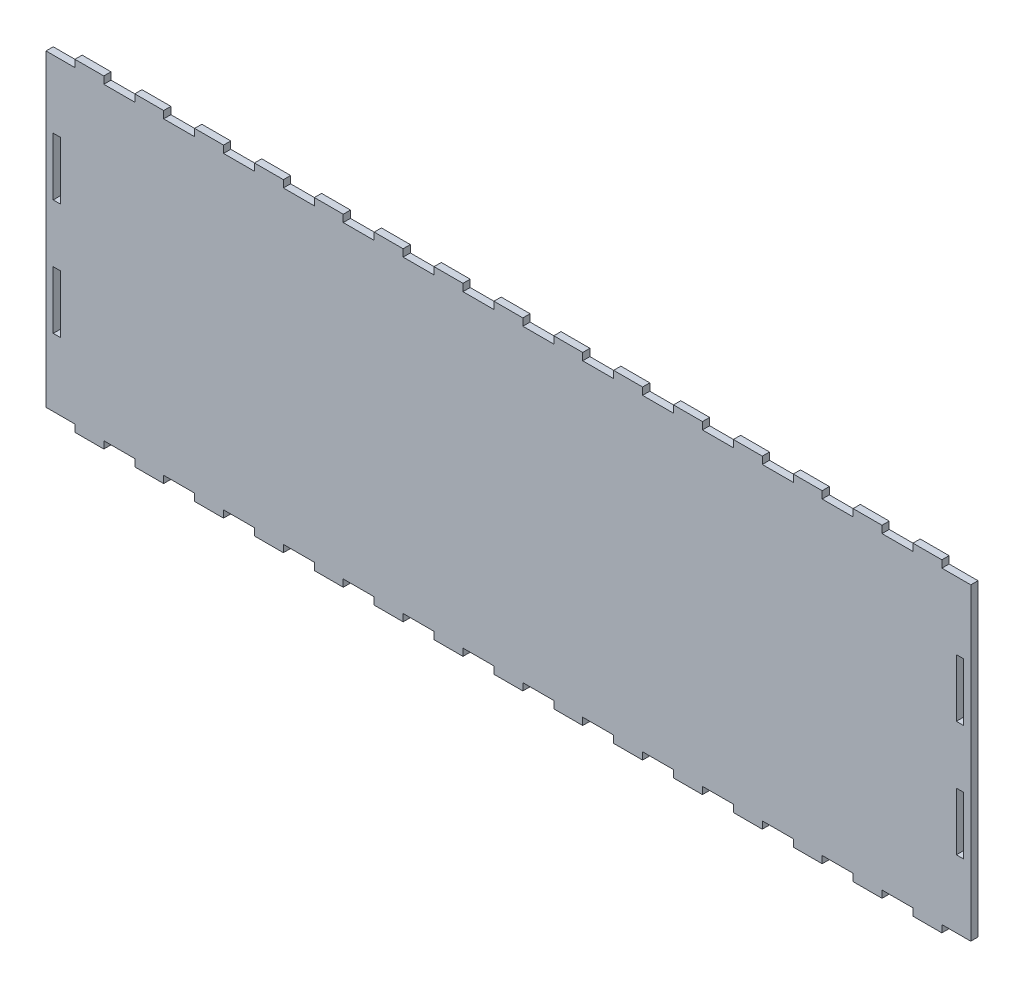
SolidWorks part; units mm, degrees
ref_plane "Front Plane" through (0, 0, 0) normal (0, 0, 1) x (1, 0, 0)
ref_plane "Top Plane" through (0, 0, 0) normal (0, 1, 0) x (1, 0, 0)
ref_plane "Right Plane" through (0, 0, 0) normal (1, 0, 0) x (0, 0, -1)
sketch "Sketch1" plane through (0, 0, 0) normal (0, 0, 1) x (1, 0, 0)
  line L8 (400.05, 105.9212) -> (400.05, 80.5212)
  line L9 (403.225, 105.9212) -> (400.05, 105.9212)
  line L10 (403.225, 80.5212) -> (403.225, 105.9212)
  line L11 (400.05, 80.5212) -> (403.225, 80.5212)
  line L16 (400.05, 55.1212) -> (400.05, 29.7212)
  line L17 (403.225, 55.1212) -> (400.05, 55.1212)
  line L18 (403.225, 29.7212) -> (403.225, 55.1212)
  line L19 (400.05, 29.7212) -> (403.225, 29.7212)
  line L24 (6.35, 80.5212) -> (6.35, 105.9212)
  line L25 (3.175, 80.5212) -> (6.35, 80.5212)
  line L26 (3.175, 105.9212) -> (3.175, 80.5212)
  line L27 (6.35, 105.9212) -> (3.175, 105.9212)
  line L32 (6.35, 29.7212) -> (6.35, 55.1212)
  line L33 (3.175, 29.7212) -> (6.35, 29.7212)
  line L34 (3.175, 55.1212) -> (3.175, 29.7212)
  line L35 (6.35, 55.1212) -> (3.175, 55.1212)
  line L400 (65.3143, 135.6423) -> (65.2143, 135.6423)
  line L401 (65.2143, 135.6423) -> (51.8071, 135.6423)
  line L402 (51.8071, 135.6423) -> (51.7071, 135.6423)
  line L403 (51.7071, 135.6423) -> (51.7071, 138.8173)
  line L404 (51.7071, 138.8173) -> (39.0071, 138.8173)
  line L405 (39.0071, 138.8173) -> (39.0071, 135.6423)
  line L406 (39.0071, 135.6423) -> (38.9071, 135.6423)
  line L407 (38.9071, 135.6423) -> (25.5, 135.6423)
  line L408 (25.5, 135.6423) -> (25.4, 135.6423)
  line L409 (25.4, 135.6423) -> (25.4, 138.8173)
  line L410 (25.4, 138.8173) -> (12.7, 138.8173)
  line L411 (12.7, 138.8173) -> (12.7, 135.6423)
  line L412 (12.7, 135.6423) -> (12.6, 135.6423)
  line L413 (12.6, 135.6423) -> (0, 135.6423)
  line L414 (0, 135.6423) -> (0, 0)
  line L415 (0, 0) -> (12.6, 0)
  line L416 (12.6, 0) -> (12.7, 0)
  line L417 (12.7, 0) -> (12.7, -3.175)
  line L418 (12.7, -3.175) -> (25.4, -3.175)
  line L419 (25.4, -3.175) -> (25.4, 0)
  line L420 (25.4, 0) -> (25.5, 0)
  line L421 (25.5, 0) -> (38.9071, 0)
  line L422 (38.9071, 0) -> (39.0071, 0)
  line L423 (39.0071, 0) -> (39.0071, -3.175)
  line L424 (39.0071, -3.175) -> (51.7071, -3.175)
  line L425 (51.7071, -3.175) -> (51.7071, 0)
  line L426 (51.7071, 0) -> (51.8071, 0)
  line L427 (51.8071, 0) -> (65.2143, 0)
  line L428 (65.2143, 0) -> (65.3143, 0)
  line L429 (65.3143, 0) -> (65.3143, -3.175)
  line L430 (65.3143, -3.175) -> (78.0143, -3.175)
  line L431 (78.0143, -3.175) -> (78.0143, 0)
  line L432 (78.0143, 0) -> (78.1143, 0)
  line L433 (78.1143, 0) -> (91.5214, 0)
  line L434 (91.5214, 0) -> (91.6214, 0)
  line L435 (91.6214, 0) -> (91.6214, -3.175)
  line L436 (91.6214, -3.175) -> (104.3214, -3.175)
  line L437 (104.3214, -3.175) -> (104.3214, 0)
  line L438 (104.3214, 0) -> (104.4214, 0)
  line L439 (104.4214, 0) -> (117.8286, 0)
  line L440 (117.8286, 0) -> (117.9286, 0)
  line L441 (117.9286, 0) -> (117.9286, -3.175)
  line L442 (117.9286, -3.175) -> (130.6286, -3.175)
  line L443 (130.6286, -3.175) -> (130.6286, 0)
  line L444 (130.6286, 0) -> (130.7286, 0)
  line L445 (130.7286, 0) -> (144.1357, 0)
  line L446 (144.1357, 0) -> (144.2357, 0)
  line L447 (144.2357, 0) -> (144.2357, -3.175)
  line L448 (144.2357, -3.175) -> (156.9357, -3.175)
  line L449 (156.9357, -3.175) -> (156.9357, 0)
  line L450 (156.9357, 0) -> (157.0357, 0)
  line L451 (157.0357, 0) -> (170.4429, 0)
  line L452 (170.4429, 0) -> (170.5429, 0)
  line L453 (170.5429, 0) -> (170.5429, -3.175)
  line L454 (170.5429, -3.175) -> (183.2429, -3.175)
  line L455 (183.2429, -3.175) -> (183.2429, 0)
  line L456 (183.2429, 0) -> (183.3429, 0)
  line L457 (183.3429, 0) -> (196.75, 0)
  line L458 (196.75, 0) -> (196.85, 0)
  line L459 (196.85, 0) -> (196.85, -3.175)
  line L460 (196.85, -3.175) -> (209.55, -3.175)
  line L461 (209.55, -3.175) -> (209.55, 0)
  line L462 (209.55, 0) -> (209.65, 0)
  line L463 (209.65, 0) -> (223.0571, 0)
  line L464 (223.0571, 0) -> (223.1571, 0)
  line L465 (223.1571, 0) -> (223.1571, -3.175)
  line L466 (223.1571, -3.175) -> (235.8571, -3.175)
  line L467 (235.8571, -3.175) -> (235.8571, 0)
  line L468 (235.8571, 0) -> (235.9571, 0)
  line L469 (235.9571, 0) -> (249.3643, 0)
  line L470 (249.3643, 0) -> (249.4643, 0)
  line L471 (249.4643, 0) -> (249.4643, -3.175)
  line L472 (249.4643, -3.175) -> (262.1643, -3.175)
  line L473 (262.1643, -3.175) -> (262.1643, 0)
  line L474 (262.1643, 0) -> (262.2643, 0)
  line L475 (262.2643, 0) -> (275.6714, 0)
  line L476 (275.6714, 0) -> (275.7714, 0)
  line L477 (275.7714, 0) -> (275.7714, -3.175)
  line L478 (275.7714, -3.175) -> (288.4714, -3.175)
  line L479 (288.4714, -3.175) -> (288.4714, 0)
  line L480 (288.4714, 0) -> (288.5714, 0)
  line L481 (288.5714, 0) -> (301.9786, 0)
  line L482 (301.9786, 0) -> (302.0786, 0)
  line L483 (302.0786, 0) -> (302.0786, -3.175)
  line L484 (302.0786, -3.175) -> (314.7786, -3.175)
  line L485 (314.7786, -3.175) -> (314.7786, 0)
  line L486 (314.7786, 0) -> (314.8786, 0)
  line L487 (314.8786, 0) -> (328.2857, 0)
  line L488 (328.2857, 0) -> (328.3857, 0)
  line L489 (328.3857, 0) -> (328.3857, -3.175)
  line L490 (328.3857, -3.175) -> (341.0857, -3.175)
  line L491 (341.0857, -3.175) -> (341.0857, 0)
  line L492 (341.0857, 0) -> (341.1857, 0)
  line L493 (341.1857, 0) -> (354.5929, 0)
  line L494 (354.5929, 0) -> (354.6929, 0)
  line L495 (354.6929, 0) -> (354.6929, -3.175)
  line L496 (354.6929, -3.175) -> (367.3929, -3.175)
  line L497 (367.3929, -3.175) -> (367.3929, 0)
  line L498 (367.3929, 0) -> (367.4929, 0)
  line L499 (367.4929, 0) -> (380.9, 0)
  line L500 (380.9, 0) -> (381, 0)
  line L501 (381, 0) -> (381, -3.175)
  line L502 (381, -3.175) -> (393.7, -3.175)
  line L503 (393.7, -3.175) -> (393.7, 0)
  line L504 (393.7, 0) -> (393.8, 0)
  line L505 (393.8, 0) -> (406.4, 0)
  line L506 (406.4, 0) -> (406.4, 135.6423)
  line L507 (406.4, 135.6423) -> (393.8, 135.6423)
  line L508 (393.8, 135.6423) -> (393.7, 135.6423)
  line L509 (393.7, 135.6423) -> (393.7, 138.8173)
  line L510 (393.7, 138.8173) -> (381, 138.8173)
  line L511 (381, 138.8173) -> (381, 135.6423)
  line L512 (381, 135.6423) -> (380.9, 135.6423)
  line L513 (380.9, 135.6423) -> (367.4929, 135.6423)
  line L514 (367.4929, 135.6423) -> (367.3929, 135.6423)
  line L515 (367.3929, 135.6423) -> (367.3929, 138.8173)
  line L516 (367.3929, 138.8173) -> (354.6929, 138.8173)
  line L517 (354.6929, 138.8173) -> (354.6929, 135.6423)
  line L518 (354.6929, 135.6423) -> (354.5929, 135.6423)
  line L519 (354.5929, 135.6423) -> (341.1857, 135.6423)
  line L520 (341.1857, 135.6423) -> (341.0857, 135.6423)
  line L521 (341.0857, 135.6423) -> (341.0857, 138.8173)
  line L522 (341.0857, 138.8173) -> (328.3857, 138.8173)
  line L523 (328.3857, 138.8173) -> (328.3857, 135.6423)
  line L524 (328.3857, 135.6423) -> (328.2857, 135.6423)
  line L525 (328.2857, 135.6423) -> (314.8786, 135.6423)
  line L526 (314.8786, 135.6423) -> (314.7786, 135.6423)
  line L527 (314.7786, 135.6423) -> (314.7786, 138.8173)
  line L528 (314.7786, 138.8173) -> (302.0786, 138.8173)
  line L529 (302.0786, 138.8173) -> (302.0786, 135.6423)
  line L530 (302.0786, 135.6423) -> (301.9786, 135.6423)
  line L531 (301.9786, 135.6423) -> (288.5714, 135.6423)
  line L532 (288.5714, 135.6423) -> (288.4714, 135.6423)
  line L533 (288.4714, 135.6423) -> (288.4714, 138.8173)
  line L534 (288.4714, 138.8173) -> (275.7714, 138.8173)
  line L535 (275.7714, 138.8173) -> (275.7714, 135.6423)
  line L536 (275.7714, 135.6423) -> (275.6714, 135.6423)
  line L537 (275.6714, 135.6423) -> (262.2643, 135.6423)
  line L538 (262.2643, 135.6423) -> (262.1643, 135.6423)
  line L539 (262.1643, 135.6423) -> (262.1643, 138.8173)
  line L540 (262.1643, 138.8173) -> (249.4643, 138.8173)
  line L541 (249.4643, 138.8173) -> (249.4643, 135.6423)
  line L542 (249.4643, 135.6423) -> (249.3643, 135.6423)
  line L543 (249.3643, 135.6423) -> (235.9571, 135.6423)
  line L544 (235.9571, 135.6423) -> (235.8571, 135.6423)
  line L545 (235.8571, 135.6423) -> (235.8571, 138.8173)
  line L546 (235.8571, 138.8173) -> (223.1571, 138.8173)
  line L547 (223.1571, 138.8173) -> (223.1571, 135.6423)
  line L548 (223.1571, 135.6423) -> (223.0571, 135.6423)
  line L549 (223.0571, 135.6423) -> (209.65, 135.6423)
  line L550 (209.65, 135.6423) -> (209.55, 135.6423)
  line L551 (209.55, 135.6423) -> (209.55, 138.8173)
  line L552 (209.55, 138.8173) -> (196.85, 138.8173)
  line L553 (196.85, 138.8173) -> (196.85, 135.6423)
  line L554 (196.85, 135.6423) -> (196.75, 135.6423)
  line L555 (196.75, 135.6423) -> (183.3429, 135.6423)
  line L556 (183.3429, 135.6423) -> (183.2429, 135.6423)
  line L557 (183.2429, 135.6423) -> (183.2429, 138.8173)
  line L558 (183.2429, 138.8173) -> (170.5429, 138.8173)
  line L559 (170.5429, 138.8173) -> (170.5429, 135.6423)
  line L560 (170.5429, 135.6423) -> (170.4429, 135.6423)
  line L561 (170.4429, 135.6423) -> (157.0357, 135.6423)
  line L562 (157.0357, 135.6423) -> (156.9357, 135.6423)
  line L563 (156.9357, 135.6423) -> (156.9357, 138.8173)
  line L564 (156.9357, 138.8173) -> (144.2357, 138.8173)
  line L565 (144.2357, 138.8173) -> (144.2357, 135.6423)
  line L566 (144.2357, 135.6423) -> (144.1357, 135.6423)
  line L567 (144.1357, 135.6423) -> (130.7286, 135.6423)
  line L568 (130.7286, 135.6423) -> (130.6286, 135.6423)
  line L569 (130.6286, 135.6423) -> (130.6286, 138.8173)
  line L570 (130.6286, 138.8173) -> (117.9286, 138.8173)
  line L571 (117.9286, 138.8173) -> (117.9286, 135.6423)
  line L572 (117.9286, 135.6423) -> (117.8286, 135.6423)
  line L573 (117.8286, 135.6423) -> (104.4214, 135.6423)
  line L574 (104.4214, 135.6423) -> (104.3214, 135.6423)
  line L575 (104.3214, 135.6423) -> (104.3214, 138.8173)
  line L576 (104.3214, 138.8173) -> (91.6214, 138.8173)
  line L577 (91.6214, 138.8173) -> (91.6214, 135.6423)
  line L578 (91.6214, 135.6423) -> (91.5214, 135.6423)
  line L579 (91.5214, 135.6423) -> (78.1143, 135.6423)
  line L580 (78.1143, 135.6423) -> (78.0143, 135.6423)
  line L581 (78.0143, 135.6423) -> (78.0143, 138.8173)
  line L582 (78.0143, 138.8173) -> (65.3143, 138.8173)
  line L583 (65.3143, 138.8173) -> (65.3143, 135.6423)
  point P18 (0, 0)
  point P20 (0, 0)
extrude "Boss-Extrude1" add sketch "Sketch1" along normal blind 3.175 contours L582 L583 L400 L401 L402 L403 L404 L405 L406 L407 L408 L409 L410 L411 L412 L413 L414 L415 L416 L417 L418 L419 L420 L421 L422 L423 L424 L425 L426 L427 L428 L429 L430 L431 L432 L433 L434 L435 L436 L437 L438 L439 L440 L441 L442 L443 L444 L445 L446 L447 L448
sketch "DXF" plane through (0, 0, 3.175) normal (0, 0, 1) x (1, 0, 0)
  line L14 (3.2766, 29.8228) -> (6.2484, 29.8228)
  line L15 (6.2484, 29.8228) -> (6.2484, 55.0196)
  line L16 (3.2766, 55.0196) -> (3.2766, 29.8228)
  line L17 (6.2484, 55.0196) -> (3.2766, 55.0196)
  line L18 (3.2766, 29.8228) -> (6.2484, 29.8228)
  line L19 (6.2484, 29.8228) -> (6.2484, 55.0196)
  line L20 (3.2766, 55.0196) -> (3.2766, 29.8228)
  line L21 (6.2484, 55.0196) -> (3.2766, 55.0196)
  line L32 (400.1516, 80.6228) -> (403.1234, 80.6228)
  line L33 (403.1234, 80.6228) -> (403.1234, 105.8196)
  line L34 (403.1234, 105.8196) -> (400.1516, 105.8196)
  line L35 (400.1516, 105.8196) -> (400.1516, 80.6228)
  line L36 (400.1516, 80.6228) -> (403.1234, 80.6228)
  line L37 (403.1234, 80.6228) -> (403.1234, 105.8196)
  line L38 (403.1234, 105.8196) -> (400.1516, 105.8196)
  line L39 (400.1516, 105.8196) -> (400.1516, 80.6228)
  line L44 (400.1516, 29.8228) -> (403.1234, 29.8228)
  line L45 (403.1234, 29.8228) -> (403.1234, 55.0196)
  line L46 (400.1516, 55.0196) -> (400.1516, 29.8228)
  line L47 (403.1234, 55.0196) -> (400.1516, 55.0196)
  line L48 (400.1516, 29.8228) -> (403.1234, 29.8228)
  line L49 (403.1234, 29.8228) -> (403.1234, 55.0196)
  line L50 (400.1516, 55.0196) -> (400.1516, 29.8228)
  line L51 (403.1234, 55.0196) -> (400.1516, 55.0196)
  line L138 (3.2766, 80.6228) -> (6.2484, 80.6228)
  line L139 (6.2484, 80.6228) -> (6.2484, 105.8196)
  line L140 (6.2484, 105.8196) -> (3.2766, 105.8196)
  line L141 (3.2766, 105.8196) -> (3.2766, 80.6228)
  line L142 (3.2766, 80.6228) -> (6.2484, 80.6228)
  line L143 (6.2484, 80.6228) -> (6.2484, 105.8196)
  line L144 (6.2484, 105.8196) -> (3.2766, 105.8196)
  line L145 (3.2766, 105.8196) -> (3.2766, 80.6228)
  line L248 (78.1159, 138.9189) -> (65.2127, 138.9189)
  line L249 (65.2127, 138.9189) -> (65.2127, 135.744)
  line L250 (65.2127, 135.744) -> (51.8087, 135.744)
  line L251 (51.8087, 135.744) -> (51.8087, 138.9189)
  line L252 (51.8087, 138.9189) -> (38.9055, 138.9189)
  line L253 (38.9055, 138.9189) -> (38.9055, 135.744)
  line L254 (38.9055, 135.744) -> (25.5016, 135.744)
  line L255 (25.5016, 135.744) -> (25.5016, 138.9189)
  line L256 (25.5016, 138.9189) -> (12.5984, 138.9189)
  line L257 (12.5984, 138.9189) -> (12.5984, 135.744)
  line L258 (12.5984, 135.744) -> (-0.1016, 135.7439)
  line L259 (-0.1016, 135.7439) -> (-0.1016, -0.1016)
  line L260 (-0.1016, -0.1016) -> (12.5984, -0.1016)
  line L261 (12.5984, -0.1016) -> (12.5984, -3.2766)
  line L262 (12.5984, -3.2766) -> (25.5016, -3.2766)
  line L263 (25.5016, -3.2766) -> (25.5016, -0.1016)
  line L264 (25.5016, -0.1016) -> (38.9055, -0.1016)
  line L265 (38.9055, -0.1016) -> (38.9055, -3.2766)
  line L266 (38.9055, -3.2766) -> (51.8087, -3.2766)
  line L267 (51.8087, -3.2766) -> (51.8087, -0.1016)
  line L268 (51.8087, -0.1016) -> (65.2127, -0.1016)
  line L269 (65.2127, -0.1016) -> (65.2127, -3.2766)
  line L270 (65.2127, -3.2766) -> (78.1159, -3.2766)
  line L271 (78.1159, -3.2766) -> (78.1159, -0.1016)
  line L272 (78.1159, -0.1016) -> (91.5198, -0.1016)
  line L273 (91.5198, -0.1016) -> (91.5198, -3.2766)
  line L274 (91.5198, -3.2766) -> (104.423, -3.2766)
  line L275 (104.423, -3.2766) -> (104.423, -0.1016)
  line L276 (104.423, -0.1016) -> (117.827, -0.1016)
  line L277 (117.827, -0.1016) -> (117.827, -3.2766)
  line L278 (117.827, -3.2766) -> (130.7302, -3.2766)
  line L279 (130.7302, -3.2766) -> (130.7302, -0.1016)
  line L280 (130.7302, -0.1016) -> (144.1341, -0.1016)
  line L281 (144.1341, -0.1016) -> (144.1341, -3.2766)
  line L282 (144.1341, -3.2766) -> (157.0373, -3.2766)
  line L283 (157.0373, -3.2766) -> (157.0373, -0.1016)
  line L284 (157.0373, -0.1016) -> (170.4413, -0.1016)
  line L285 (170.4413, -0.1016) -> (170.4413, -3.2766)
  line L286 (170.4413, -3.2766) -> (183.3445, -3.2766)
  line L287 (183.3445, -3.2766) -> (183.3445, -0.1016)
  line L288 (183.3445, -0.1016) -> (196.7484, -0.1016)
  line L289 (196.7484, -0.1016) -> (196.7484, -3.2766)
  line L290 (196.7484, -3.2766) -> (209.6516, -3.2766)
  line L291 (209.6516, -3.2766) -> (209.6516, -0.1016)
  line L292 (209.6516, -0.1016) -> (223.0555, -0.1016)
  line L293 (223.0555, -0.1016) -> (223.0555, -3.2766)
  line L294 (223.0555, -3.2766) -> (235.9587, -3.2766)
  line L295 (235.9587, -3.2766) -> (235.9587, -0.1016)
  line L296 (235.9587, -0.1016) -> (249.3627, -0.1016)
  line L297 (249.3627, -0.1016) -> (249.3627, -3.2766)
  line L298 (249.3627, -3.2766) -> (262.2659, -3.2766)
  line L299 (262.2659, -3.2766) -> (262.2659, -0.1016)
  line L300 (262.2659, -0.1016) -> (275.6698, -0.1016)
  line L301 (275.6698, -0.1016) -> (275.6698, -3.2766)
  line L302 (275.6698, -3.2766) -> (288.573, -3.2766)
  line L303 (288.573, -3.2766) -> (288.573, -0.1016)
  line L304 (288.573, -0.1016) -> (301.977, -0.1016)
  line L305 (301.977, -0.1016) -> (301.977, -3.2766)
  line L306 (301.977, -3.2766) -> (314.8802, -3.2766)
  line L307 (314.8802, -3.2766) -> (314.8802, -0.1016)
  line L308 (314.8802, -0.1016) -> (328.2841, -0.1016)
  line L309 (328.2841, -0.1016) -> (328.2841, -3.2766)
  line L310 (328.2841, -3.2766) -> (341.1873, -3.2766)
  line L311 (341.1873, -3.2766) -> (341.1873, -0.1016)
  line L312 (341.1873, -0.1016) -> (354.5913, -0.1016)
  line L313 (354.5913, -0.1016) -> (354.5913, -3.2766)
  line L314 (354.5913, -3.2766) -> (367.4945, -3.2766)
  line L315 (367.4945, -3.2766) -> (367.4945, -0.1016)
  line L316 (367.4945, -0.1016) -> (380.8984, -0.1016)
  line L317 (380.8984, -0.1016) -> (380.8984, -3.2766)
  line L318 (380.8984, -3.2766) -> (393.8016, -3.2766)
  line L319 (393.8016, -3.2766) -> (393.8016, -0.1016)
  line L320 (393.8016, -0.1016) -> (406.5016, -0.1016)
  line L321 (406.5016, -0.1016) -> (406.5016, 135.744)
  line L322 (406.5016, 135.744) -> (393.8016, 135.744)
  line L323 (393.8016, 135.744) -> (393.8016, 138.9189)
  line L324 (393.8016, 138.9189) -> (380.8984, 138.9189)
  line L325 (380.8984, 138.9189) -> (380.8984, 135.744)
  line L326 (380.8984, 135.744) -> (367.4945, 135.744)
  line L327 (367.4945, 135.744) -> (367.4945, 138.9189)
  line L328 (367.4945, 138.9189) -> (354.5913, 138.9189)
  line L329 (354.5913, 138.9189) -> (354.5913, 135.744)
  line L330 (354.5913, 135.744) -> (341.1873, 135.744)
  line L331 (341.1873, 135.744) -> (341.1873, 138.9189)
  line L332 (341.1873, 138.9189) -> (328.2841, 138.9189)
  line L333 (328.2841, 138.9189) -> (328.2841, 135.744)
  line L334 (328.2841, 135.744) -> (314.8802, 135.744)
  line L335 (314.8802, 135.744) -> (314.8802, 138.9189)
  line L336 (314.8802, 138.9189) -> (301.977, 138.9189)
  line L337 (301.977, 138.9189) -> (301.977, 135.744)
  line L338 (301.977, 135.744) -> (288.573, 135.744)
  line L339 (288.573, 135.744) -> (288.573, 138.9189)
  line L340 (288.573, 138.9189) -> (275.6698, 138.9189)
  line L341 (275.6698, 138.9189) -> (275.6698, 135.744)
  line L342 (275.6698, 135.744) -> (262.2659, 135.744)
  line L343 (262.2659, 135.744) -> (262.2659, 138.9189)
  line L344 (262.2659, 138.9189) -> (249.3627, 138.9189)
  line L345 (249.3627, 138.9189) -> (249.3627, 135.744)
  line L346 (249.3627, 135.744) -> (235.9587, 135.744)
  line L347 (235.9587, 135.744) -> (235.9587, 138.9189)
  line L348 (235.9587, 138.9189) -> (223.0555, 138.9189)
  line L349 (223.0555, 138.9189) -> (223.0555, 135.744)
  line L350 (223.0555, 135.744) -> (209.6516, 135.744)
  line L351 (209.6516, 135.744) -> (209.6516, 138.9189)
  line L352 (209.6516, 138.9189) -> (196.7484, 138.9189)
  line L353 (196.7484, 138.9189) -> (196.7484, 135.744)
  line L354 (196.7484, 135.744) -> (183.3445, 135.744)
  line L355 (183.3445, 135.744) -> (183.3445, 138.9189)
  line L356 (183.3445, 138.9189) -> (170.4413, 138.9189)
  line L357 (170.4413, 138.9189) -> (170.4413, 135.744)
  line L358 (170.4413, 135.744) -> (157.0373, 135.744)
  line L359 (157.0373, 135.744) -> (157.0373, 138.9189)
  line L360 (157.0373, 138.9189) -> (144.1341, 138.9189)
  line L361 (144.1341, 138.9189) -> (144.1341, 135.744)
  line L362 (144.1341, 135.744) -> (130.7302, 135.744)
  line L363 (130.7302, 135.744) -> (130.7302, 138.9189)
  line L364 (130.7302, 138.9189) -> (117.827, 138.9189)
  line L365 (117.827, 138.9189) -> (117.827, 135.744)
  line L366 (117.827, 135.744) -> (104.423, 135.744)
  line L367 (104.423, 135.744) -> (104.423, 138.9189)
  line L368 (104.423, 138.9189) -> (91.5198, 138.9189)
  line L369 (91.5198, 138.9189) -> (91.5198, 135.744)
  line L370 (91.5198, 135.744) -> (78.1159, 135.744)
  line L371 (78.1159, 135.744) -> (78.1159, 138.9189)
  line L372 (78.1159, 138.9189) -> (65.2127, 138.9189)
  line L373 (65.2127, 138.9189) -> (65.2127, 135.744)
  line L374 (65.2127, 135.744) -> (51.8087, 135.744)
  line L375 (51.8087, 135.744) -> (51.8087, 138.9189)
  line L376 (51.8087, 138.9189) -> (38.9055, 138.9189)
  line L377 (38.9055, 138.9189) -> (38.9055, 135.744)
  line L378 (38.9055, 135.744) -> (25.5016, 135.744)
  line L379 (25.5016, 135.744) -> (25.5016, 138.9189)
  line L380 (25.5016, 138.9189) -> (12.5984, 138.9189)
  line L381 (12.5984, 138.9189) -> (12.5984, 135.744)
  line L382 (12.5984, 135.744) -> (-0.1016, 135.7439)
  line L383 (-0.1016, 135.7439) -> (-0.1016, -0.1016)
  line L384 (-0.1016, -0.1016) -> (12.5984, -0.1016)
  line L385 (12.5984, -0.1016) -> (12.5984, -3.2766)
  line L386 (12.5984, -3.2766) -> (25.5016, -3.2766)
  line L387 (25.5016, -3.2766) -> (25.5016, -0.1016)
  line L388 (25.5016, -0.1016) -> (38.9055, -0.1016)
  line L389 (38.9055, -0.1016) -> (38.9055, -3.2766)
  line L390 (38.9055, -3.2766) -> (51.8087, -3.2766)
  line L391 (51.8087, -3.2766) -> (51.8087, -0.1016)
  line L392 (51.8087, -0.1016) -> (65.2127, -0.1016)
  line L393 (65.2127, -0.1016) -> (65.2127, -3.2766)
  line L394 (65.2127, -3.2766) -> (78.1159, -3.2766)
  line L395 (78.1159, -3.2766) -> (78.1159, -0.1016)
  line L396 (78.1159, -0.1016) -> (91.5198, -0.1016)
  line L397 (91.5198, -0.1016) -> (91.5198, -3.2766)
  line L398 (91.5198, -3.2766) -> (104.423, -3.2766)
  line L399 (104.423, -3.2766) -> (104.423, -0.1016)
  line L400 (104.423, -0.1016) -> (117.827, -0.1016)
  line L401 (117.827, -0.1016) -> (117.827, -3.2766)
  line L402 (117.827, -3.2766) -> (130.7302, -3.2766)
  line L403 (130.7302, -3.2766) -> (130.7302, -0.1016)
  line L404 (130.7302, -0.1016) -> (144.1341, -0.1016)
  line L405 (144.1341, -0.1016) -> (144.1341, -3.2766)
  line L406 (144.1341, -3.2766) -> (157.0373, -3.2766)
  line L407 (157.0373, -3.2766) -> (157.0373, -0.1016)
  line L408 (157.0373, -0.1016) -> (170.4413, -0.1016)
  line L409 (170.4413, -0.1016) -> (170.4413, -3.2766)
  line L410 (170.4413, -3.2766) -> (183.3445, -3.2766)
  line L411 (183.3445, -3.2766) -> (183.3445, -0.1016)
  line L412 (183.3445, -0.1016) -> (196.7484, -0.1016)
  line L413 (196.7484, -0.1016) -> (196.7484, -3.2766)
  line L414 (196.7484, -3.2766) -> (209.6516, -3.2766)
  line L415 (209.6516, -3.2766) -> (209.6516, -0.1016)
  line L416 (209.6516, -0.1016) -> (223.0555, -0.1016)
  line L417 (223.0555, -0.1016) -> (223.0555, -3.2766)
  line L418 (223.0555, -3.2766) -> (235.9587, -3.2766)
  line L419 (235.9587, -3.2766) -> (235.9587, -0.1016)
  line L420 (235.9587, -0.1016) -> (249.3627, -0.1016)
  line L421 (249.3627, -0.1016) -> (249.3627, -3.2766)
  line L422 (249.3627, -3.2766) -> (262.2659, -3.2766)
  line L423 (262.2659, -3.2766) -> (262.2659, -0.1016)
  line L424 (262.2659, -0.1016) -> (275.6698, -0.1016)
  line L425 (275.6698, -0.1016) -> (275.6698, -3.2766)
  line L426 (275.6698, -3.2766) -> (288.573, -3.2766)
  line L427 (288.573, -3.2766) -> (288.573, -0.1016)
  line L428 (288.573, -0.1016) -> (301.977, -0.1016)
  line L429 (301.977, -0.1016) -> (301.977, -3.2766)
  line L430 (301.977, -3.2766) -> (314.8802, -3.2766)
  line L431 (314.8802, -3.2766) -> (314.8802, -0.1016)
  line L432 (314.8802, -0.1016) -> (328.2841, -0.1016)
  line L433 (328.2841, -0.1016) -> (328.2841, -3.2766)
  line L434 (328.2841, -3.2766) -> (341.1873, -3.2766)
  line L435 (341.1873, -3.2766) -> (341.1873, -0.1016)
  line L436 (341.1873, -0.1016) -> (354.5913, -0.1016)
  line L437 (354.5913, -0.1016) -> (354.5913, -3.2766)
  line L438 (354.5913, -3.2766) -> (367.4945, -3.2766)
  line L439 (367.4945, -3.2766) -> (367.4945, -0.1016)
  line L440 (367.4945, -0.1016) -> (380.8984, -0.1016)
  line L441 (380.8984, -0.1016) -> (380.8984, -3.2766)
  line L442 (380.8984, -3.2766) -> (393.8016, -3.2766)
  line L443 (393.8016, -3.2766) -> (393.8016, -0.1016)
  line L444 (393.8016, -0.1016) -> (406.5016, -0.1016)
  line L445 (406.5016, -0.1016) -> (406.5016, 135.744)
  line L446 (406.5016, 135.744) -> (393.8016, 135.744)
  line L447 (393.8016, 135.744) -> (393.8016, 138.9189)
  line L448 (393.8016, 138.9189) -> (380.8984, 138.9189)
  line L449 (380.8984, 138.9189) -> (380.8984, 135.744)
  line L450 (380.8984, 135.744) -> (367.4945, 135.744)
  line L451 (367.4945, 135.744) -> (367.4945, 138.9189)
  line L452 (367.4945, 138.9189) -> (354.5913, 138.9189)
  line L453 (354.5913, 138.9189) -> (354.5913, 135.744)
  line L454 (354.5913, 135.744) -> (341.1873, 135.744)
  line L455 (341.1873, 135.744) -> (341.1873, 138.9189)
  line L456 (341.1873, 138.9189) -> (328.2841, 138.9189)
  line L457 (328.2841, 138.9189) -> (328.2841, 135.744)
  line L458 (328.2841, 135.744) -> (314.8802, 135.744)
  line L459 (314.8802, 135.744) -> (314.8802, 138.9189)
  line L460 (314.8802, 138.9189) -> (301.977, 138.9189)
  line L461 (301.977, 138.9189) -> (301.977, 135.744)
  line L462 (301.977, 135.744) -> (288.573, 135.744)
  line L463 (288.573, 135.744) -> (288.573, 138.9189)
  line L464 (288.573, 138.9189) -> (275.6698, 138.9189)
  line L465 (275.6698, 138.9189) -> (275.6698, 135.744)
  line L466 (275.6698, 135.744) -> (262.2659, 135.744)
  line L467 (262.2659, 135.744) -> (262.2659, 138.9189)
  line L468 (262.2659, 138.9189) -> (249.3627, 138.9189)
  line L469 (249.3627, 138.9189) -> (249.3627, 135.744)
  line L470 (249.3627, 135.744) -> (235.9587, 135.744)
  line L471 (235.9587, 135.744) -> (235.9587, 138.9189)
  line L472 (235.9587, 138.9189) -> (223.0555, 138.9189)
  line L473 (223.0555, 138.9189) -> (223.0555, 135.744)
  line L474 (223.0555, 135.744) -> (209.6516, 135.744)
  line L475 (209.6516, 135.744) -> (209.6516, 138.9189)
  line L476 (209.6516, 138.9189) -> (196.7484, 138.9189)
  line L477 (196.7484, 138.9189) -> (196.7484, 135.744)
  line L478 (196.7484, 135.744) -> (183.3445, 135.744)
  line L479 (183.3445, 135.744) -> (183.3445, 138.9189)
  line L480 (183.3445, 138.9189) -> (170.4413, 138.9189)
  line L481 (170.4413, 138.9189) -> (170.4413, 135.744)
  line L482 (170.4413, 135.744) -> (157.0373, 135.744)
  line L483 (157.0373, 135.744) -> (157.0373, 138.9189)
  line L484 (157.0373, 138.9189) -> (144.1341, 138.9189)
  line L485 (144.1341, 138.9189) -> (144.1341, 135.744)
  line L486 (144.1341, 135.744) -> (130.7302, 135.744)
  line L487 (130.7302, 135.744) -> (130.7302, 138.9189)
  line L488 (130.7302, 138.9189) -> (117.827, 138.9189)
  line L489 (117.827, 138.9189) -> (117.827, 135.744)
  line L490 (117.827, 135.744) -> (104.423, 135.744)
  line L491 (104.423, 135.744) -> (104.423, 138.9189)
  line L492 (104.423, 138.9189) -> (91.5198, 138.9189)
  line L493 (91.5198, 138.9189) -> (91.5198, 135.744)
  line L494 (91.5198, 135.744) -> (78.1159, 135.744)
  line L495 (78.1159, 135.744) -> (78.1159, 138.9189)
  dimension "D1" = 0.1016
  dimension "D2" = 0.1016
  dimension "D3" = 0.1016
  dimension "D4" = 0.1016
  dimension "D5" = 0.1016
extrude "DXF-Extrude" [suppressed] add sketch "DXF" against normal blind 3.175
